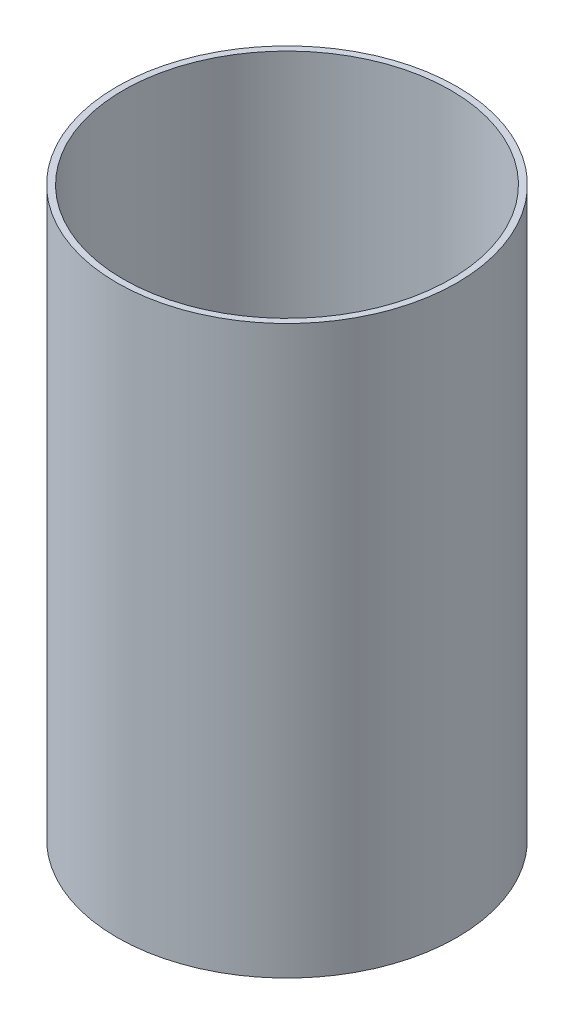
SolidWorks part; units mm, degrees
material "E-Glass Fiber"
ref_plane "Front Plane" through (0, 0, 0) normal (0, 0, 1) x (1, 0, 0)
ref_plane "Top Plane" through (0, 0, 0) normal (0, 1, 0) x (1, 0, 0)
ref_plane "Right Plane" through (0, 0, 0) normal (1, 0, 0) x (0, 0, -1)
sketch "Coupler Profile" plane through (0, 0, 0) normal (0, 1, 0) x (1, 0, 0)
  circle A0 centre (0, 0) radius 73.3425
  circle A1 centre (0, 0) radius 76.1746
  dimension "D1" = 146.685
  dimension "D2" = 152.3492
extrude "Coupler Body" add sketch "Coupler Profile" along normal blind 254
equation "\"Length\"= 10"
equation "\"Outer Diameter\"= 5.998"
equation "\"Inner Diameter\"= 5.775"
equation "\"Wall Thickness\"= 0.111"
equation "\"D1@Coupler Profile\" = \"Inner Diameter\""
equation "\"D2@Coupler Profile\" = \"Outer Diameter\""
equation "\"D1@Coupler Body\" = \"Length\""
